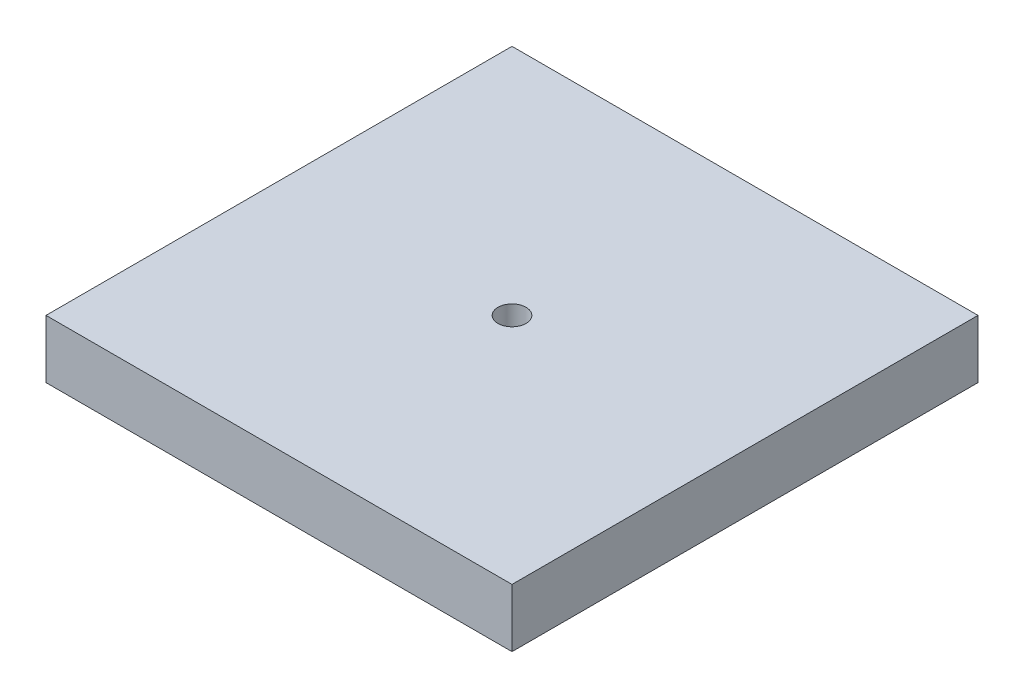
SolidWorks part; units mm, degrees
ref_plane "Front Plane" through (0, 0, 0) normal (0, 0, 1) x (1, 0, 0)
ref_plane "Top Plane" through (0, 0, 0) normal (0, 1, 0) x (1, 0, 0)
ref_plane "Right Plane" through (0, 0, 0) normal (1, 0, 0) x (0, 0, -1)
sketch "Sketch1" plane through (0, 0, 0) normal (0, 1, 0) x (1, 0, 0)
  line L1 (-20, -20) -> (20, -20)
  line L2 (-20, -20) -> (-20, 20)
  line L3 (-20, 20) -> (20, 20)
  line L4 (20, -20) -> (20, 20)
  line L5 (-20, -20) -> (20, 20) construction
  line L6 (-20, 20) -> (20, -20) construction
  circle A0 centre (0, 0) radius 1.205
  point P0 (0, 0)
  dimension "D3" = 2.41
  dimension "D1" = 40
  dimension "D2" = 40
extrude "Boss-Extrude1" add sketch "Sketch1" along normal blind 5
